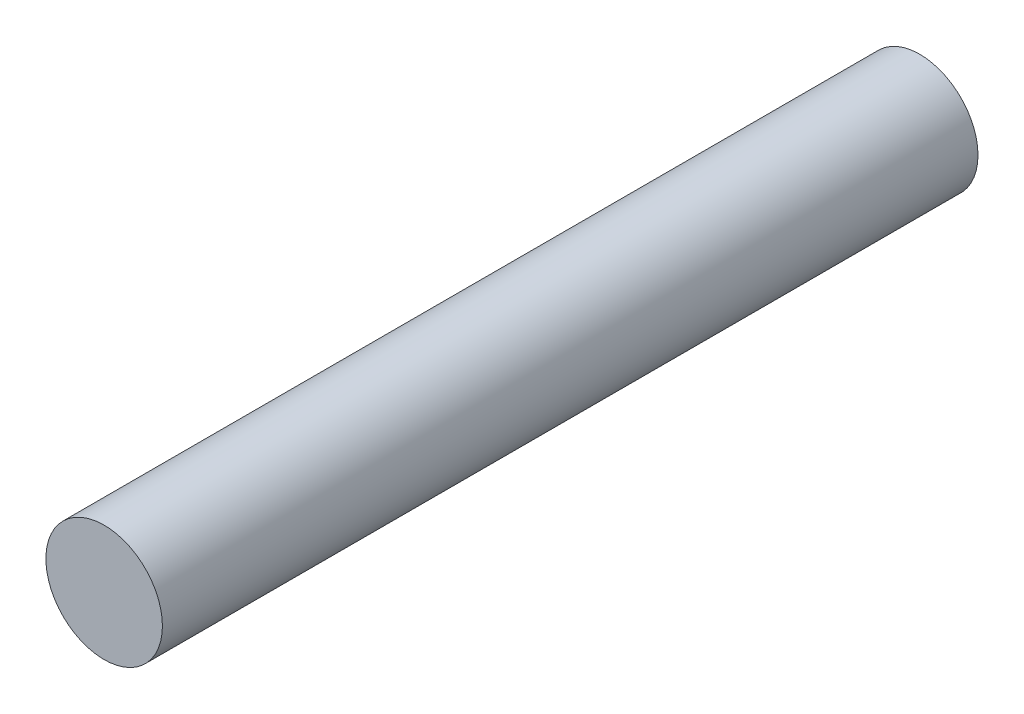
SolidWorks part; units mm, degrees
ref_plane "Front Plane" through (0, 0, 0) normal (0, 0, 1) x (1, 0, 0)
ref_plane "Top Plane" through (0, 0, 0) normal (0, 1, 0) x (1, 0, 0)
ref_plane "Right Plane" through (0, 0, 0) normal (1, 0, 0) x (0, 0, -1)
sketch "Sketch1" plane through (0, 0, 0) normal (0, 0, 1) x (1, 0, 0)
  circle A0 centre (0, 0) radius 2
  dimension "D1" = 4
extrude "Boss-Extrude1" add sketch "Sketch1" along normal mid plane 28
